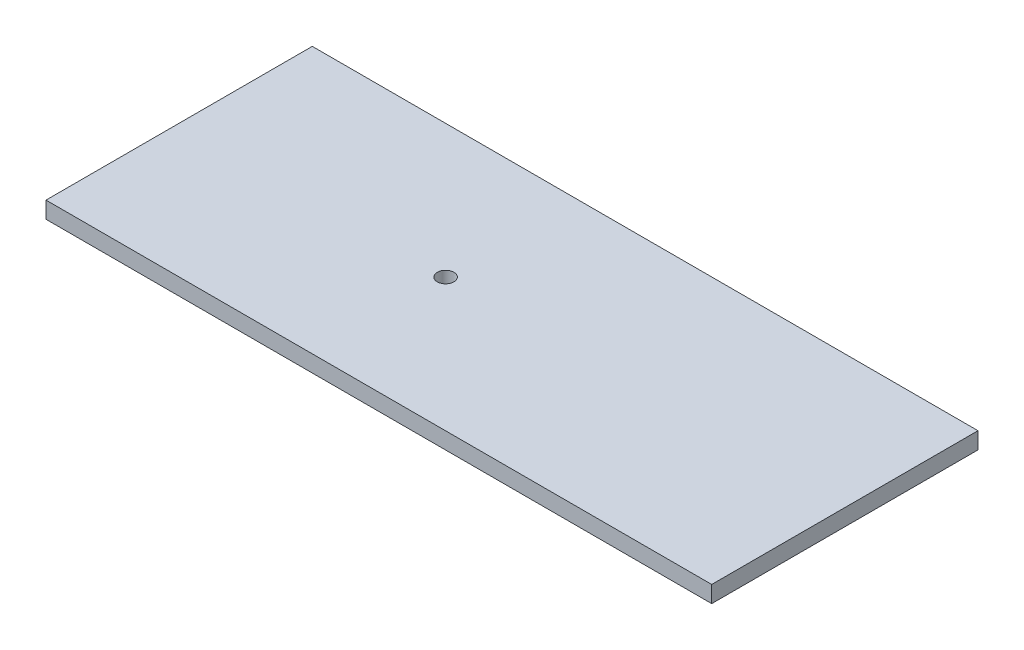
SolidWorks part; units mm, degrees
material "Oak"
ref_plane "Front Plane" through (0, 0, 0) normal (0, 0, 1) x (1, 0, 0)
ref_plane "Top Plane" through (0, 0, 0) normal (0, 1, 0) x (1, 0, 0)
ref_plane "Right Plane" through (0, 0, 0) normal (1, 0, 0) x (0, 0, -1)
sketch "Sketch1" plane through (0, 0, 0) normal (0, 1, 0) x (1, 0, 0)
  line L1 (-762, 304.8) -> (762, 304.8)
  line L2 (-762, 304.8) -> (-762, -304.8)
  line L3 (-762, -304.8) -> (762, -304.8)
  line L4 (762, 304.8) -> (762, -304.8)
  line L5 (-762, 304.8) -> (762, -304.8) construction
  line L6 (-762, -304.8) -> (762, 304.8) construction
  point P0 (0, 0)
  dimension "D1" = 609.6
  dimension "D2" = 1524
extrude "Boss-Extrude1" add sketch "Sketch1" against normal blind 38.1
sketch "Sketch2" plane through (0, 0, 0) normal (0, 1, 0) x (1, 0, 0)
  line L0 (-762, 304.8) -> (-762, -304.8) construction
  circle A0 centre (-152, 0) radius 19.05
  point P2 (-403.9379, -60.5965)
  dimension "D1" = 38.1
  dimension "D2" = 610
extrude "Cut-Extrude1" cut sketch "Sketch2" against normal through all
